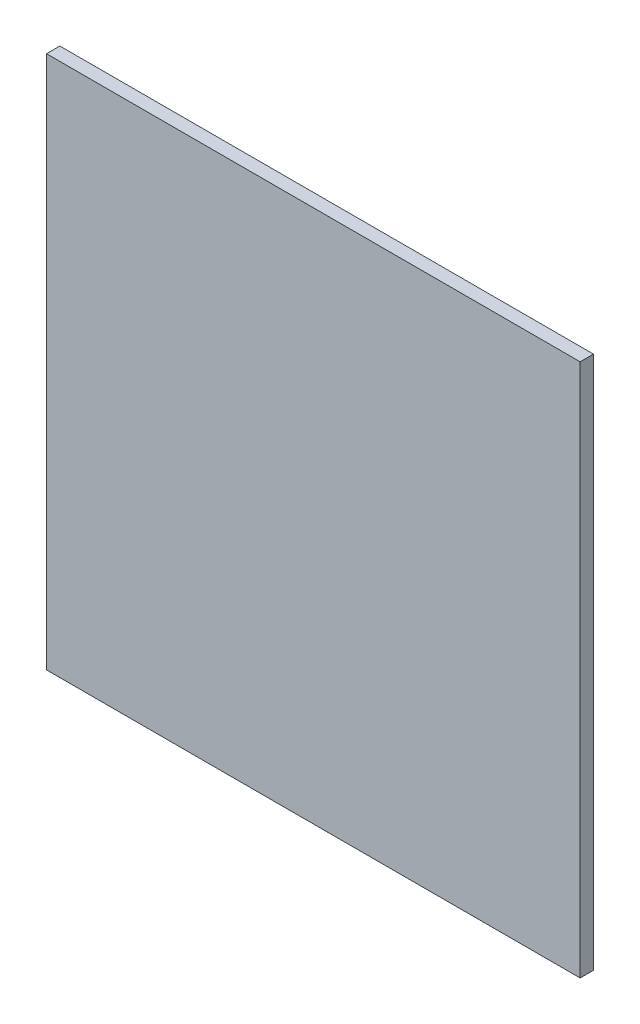
SolidWorks part; units mm, degrees
ref_plane "Front Plane" through (0, 0, 0) normal (0, 0, 1) x (1, 0, 0)
ref_plane "Top Plane" through (0, 0, 0) normal (0, 1, 0) x (1, 0, 0)
ref_plane "Right Plane" through (0, 0, 0) normal (1, 0, 0) x (0, 0, -1)
sketch "Sketch1" plane through (0, 0, 0) normal (0, 0, 1) x (1, 0, 0)
  line L1 (-1, -1) -> (1, -1)
  line L2 (-1, -1) -> (-1, 1)
  line L3 (-1, 1) -> (1, 1)
  line L4 (1, -1) -> (1, 1)
  line L5 (-1, -1) -> (1, 1) construction
  line L6 (-1, 1) -> (1, -1) construction
  point P0 (0, 0)
  dimension "D1" = 2
  dimension "D2" = 2
extrude "Boss-Extrude1" add sketch "Sketch1" along normal blind 0.05
